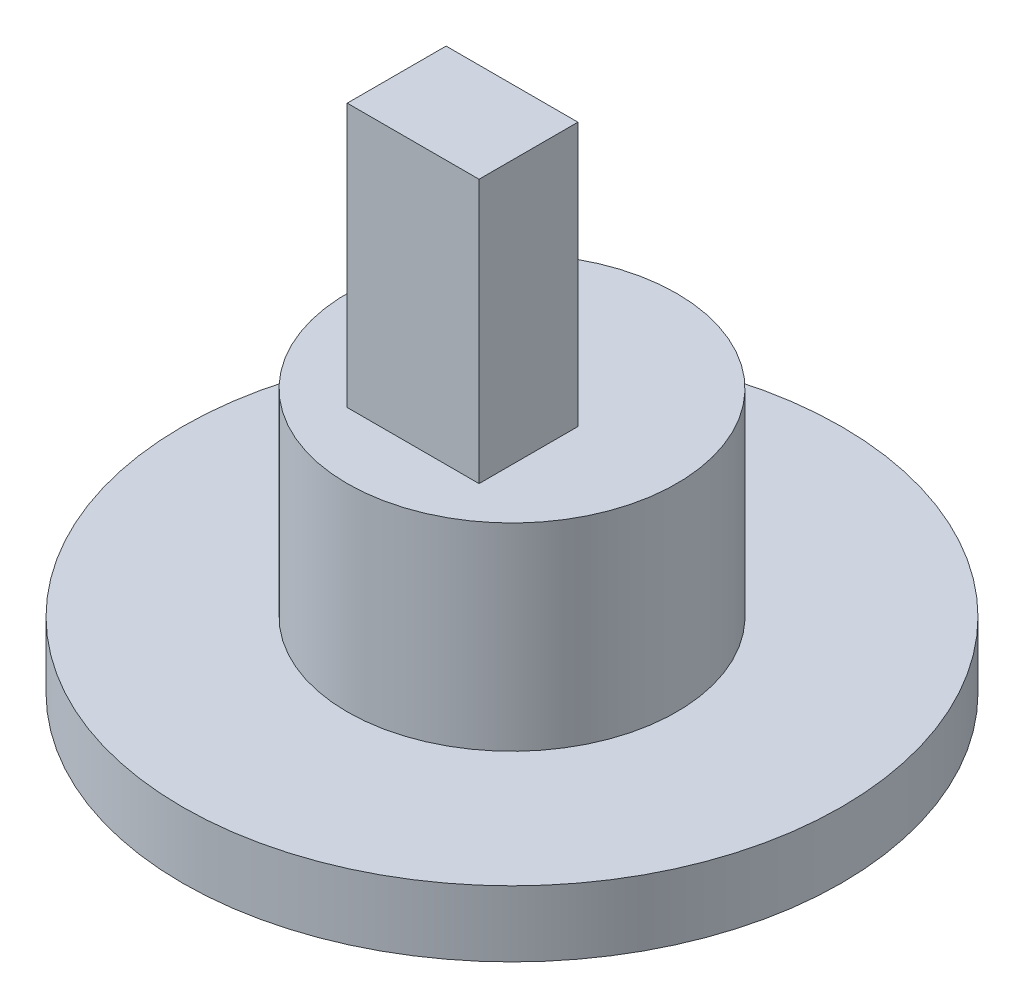
SolidWorks part; units mm, degrees
ref_plane "Front Plane" through (0, 0, 0) normal (0, 0, 1) x (1, 0, 0)
ref_plane "Top Plane" through (0, 0, 0) normal (0, 1, 0) x (1, 0, 0)
ref_plane "Right Plane" through (0, 0, 0) normal (1, 0, 0) x (0, 0, -1)
sketch "Sketch1" plane through (0, 0, 0) normal (0, 1, 0) x (1, 0, 0)
  circle A0 centre (0, 0) radius 5
  dimension "D1" = 10
extrude "Boss-Extrude1" add sketch "Sketch1" along normal blind 6
sketch "Sketch3" plane through (0, 6, 0) normal (0, 1, 0) x (1, 0, 0)
  line L1 (-2, -3) -> (2, -3)
  line L2 (-2, -3) -> (-2, 0)
  line L3 (-2, 0) -> (2, 0)
  line L4 (2, -3) -> (2, 0)
  line L5 (-2, -3) -> (2, 0) construction
  line L6 (-2, 0) -> (2, -3) construction
  point P0 (0, -1.5)
  point P5 (0, 0)
  dimension "D1" = 4
  dimension "D2" = 3
  dimension "D3" = 1.5
extrude "Boss-Extrude2" add sketch "Sketch3" along normal blind 8
sketch "Sketch4" plane through (0, 0, 0) normal (0, -1, 0) x (1, 0, 0)
  circle A0 centre (0, 0) radius 10
  dimension "D1" = 20
extrude "Boss-Extrude3" add sketch "Sketch4" along normal blind 2
